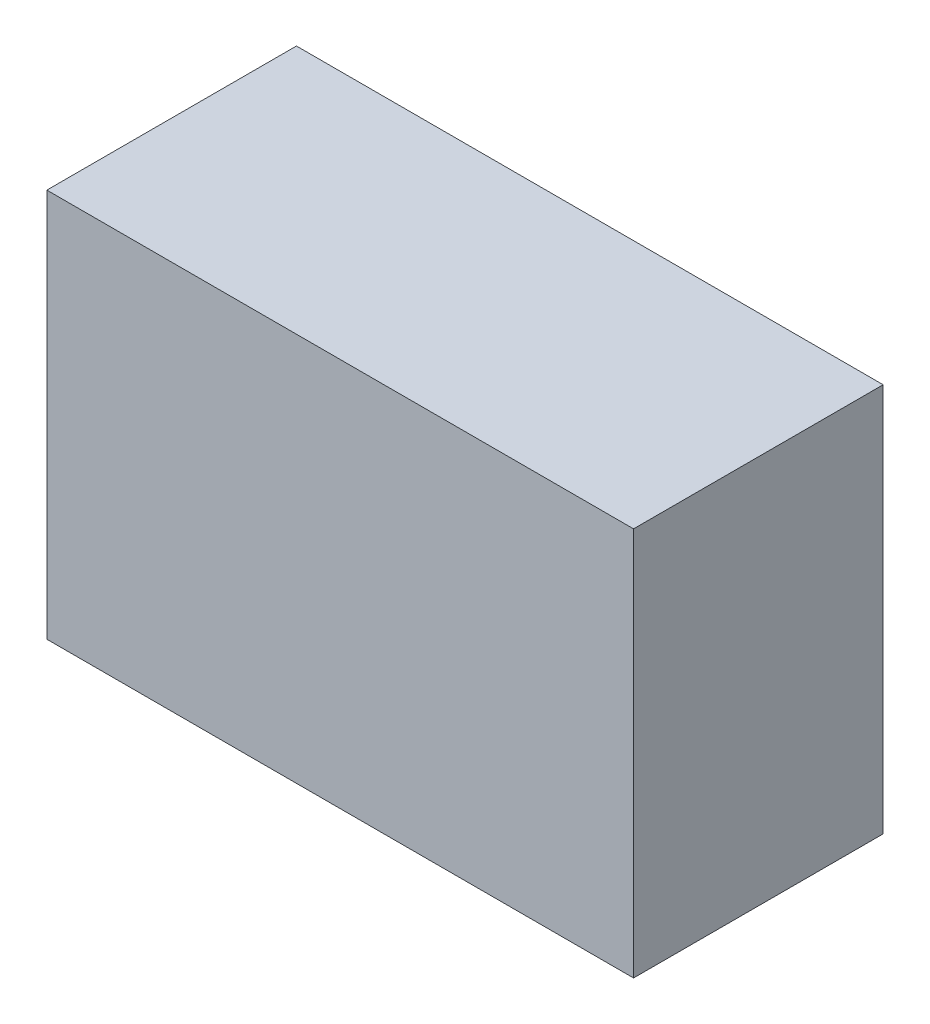
SolidWorks part; units mm, degrees
ref_plane "Plano frontal" through (0, 0, 0) normal (0, 0, 1) x (1, 0, 0)
ref_plane "Plano superior" through (0, 0, 0) normal (0, 1, 0) x (1, 0, 0)
ref_plane "Plano direito" through (0, 0, 0) normal (1, 0, 0) x (0, 0, -1)
sketch "Esboço1" plane through (0, 0, 0) normal (0, 0, 1) x (1, 0, 0)
  line L1 (-41.9136, 28.0949) -> (48.5864, 28.0949)
  line L2 (-41.9136, 28.0949) -> (-41.9136, -31.9051)
  line L3 (-41.9136, -31.9051) -> (48.5864, -31.9051)
  line L4 (48.5864, 28.0949) -> (48.5864, -31.9051)
  dimension "D1" = 90.5
  dimension "D2" = 60
extrude "Ressalto-extrusão1" add sketch "Esboço1" along normal blind 38.5
